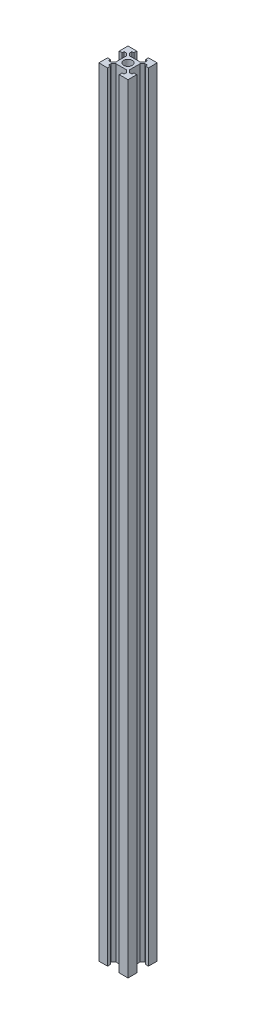
SolidWorks part; units mm, degrees
ref_plane "Front Plane" through (0, 0, 0) normal (0, 0, 1) x (1, 0, 0)
ref_plane "Top Plane" through (0, 0, 0) normal (0, 1, 0) x (1, 0, 0)
ref_plane "Right Plane" through (0, 0, 0) normal (1, 0, 0) x (0, 0, -1)
sketch "Sketch1" plane through (0, 0, 0) normal (0, 1, 0) x (1, 0, 0)
  line L0 (-30, 0) -> (30, 0) construction
  line L3 (-30, 30) -> (-12, 30)
  line L5 (-30, -30) -> (30, 30) construction
  line L6 (-30, 30) -> (30, -30) construction
  line L7 (0, 30) -> (0, -30) construction
  line L8 (-30, 12) -> (-24, 12)
  line L13 (-24, -24) -> (24, 24) construction
  line L14 (-24, 24) -> (24, -24) construction
  line L15 (-14, 24) -> (-14, 16) construction
  line L16 (-24, 16) -> (-19, 16)
  line L17 (-19, 16) -> (-14, 11)
  line L18 (-30, 12) -> (-30, 30)
  line L19 (-14, 11) -> (-14, -11)
  line L20 (-24, 12) -> (-24, 16)
  line L21 (-11, 14) -> (11, 14)
  line L22 (-16, 19) -> (-11, 14)
  line L23 (-12, 24) -> (-16, 24)
  line L24 (-16, 24) -> (-16, 19)
  line L25 (-12, 30) -> (-12, 24)
  line L26 (12, 30) -> (30, 30)
  line L27 (12, 30) -> (12, 24)
  line L28 (12, 24) -> (16, 24)
  line L29 (16, 24) -> (16, 19)
  line L30 (16, 19) -> (11, 14)
  line L31 (14, 11) -> (14, -11)
  line L32 (19, 16) -> (14, 11)
  line L33 (24, 12) -> (24, 16)
  line L34 (24, 16) -> (19, 16)
  line L35 (30, 12) -> (24, 12)
  line L36 (30, 12) -> (30, 30)
  line L37 (-14, -24) -> (-14, -16) construction
  line L38 (30, -12) -> (30, -30)
  line L39 (30, -12) -> (24, -12)
  line L40 (24, -16) -> (19, -16)
  line L41 (24, -12) -> (24, -16)
  line L42 (19, -16) -> (14, -11)
  line L43 (16, -19) -> (11, -14)
  line L44 (16, -24) -> (16, -19)
  line L45 (12, -24) -> (16, -24)
  line L46 (12, -30) -> (12, -24)
  line L47 (12, -30) -> (30, -30)
  line L48 (-12, -30) -> (-12, -24)
  line L49 (-16, -24) -> (-16, -19)
  line L50 (-12, -24) -> (-16, -24)
  line L51 (-16, -19) -> (-11, -14)
  line L52 (-11, -14) -> (11, -14)
  line L53 (-24, -12) -> (-24, -16)
  line L54 (-30, -12) -> (-30, -30)
  line L55 (-19, -16) -> (-14, -11)
  line L56 (-24, -16) -> (-19, -16)
  line L57 (-30, -12) -> (-24, -12)
  line L58 (-30, -30) -> (-12, -30)
  circle A0 centre (0, 0) radius 9
  point P0 (0, 0)
  point P10 (0, 0)
  point P34 (0, 14)
  point P41 (-14, 0)
  point P42 (14, 0)
  point P62 (0, -14)
  dimension "D1" = 18
  dimension "D3" = 12
  dimension "D5" = 16
  dimension "D6" = 5
  dimension "D7" = 5
  dimension "D8" = 6
extrude "Boss-Extrude1" add sketch "Sketch1" along normal blind 1600
